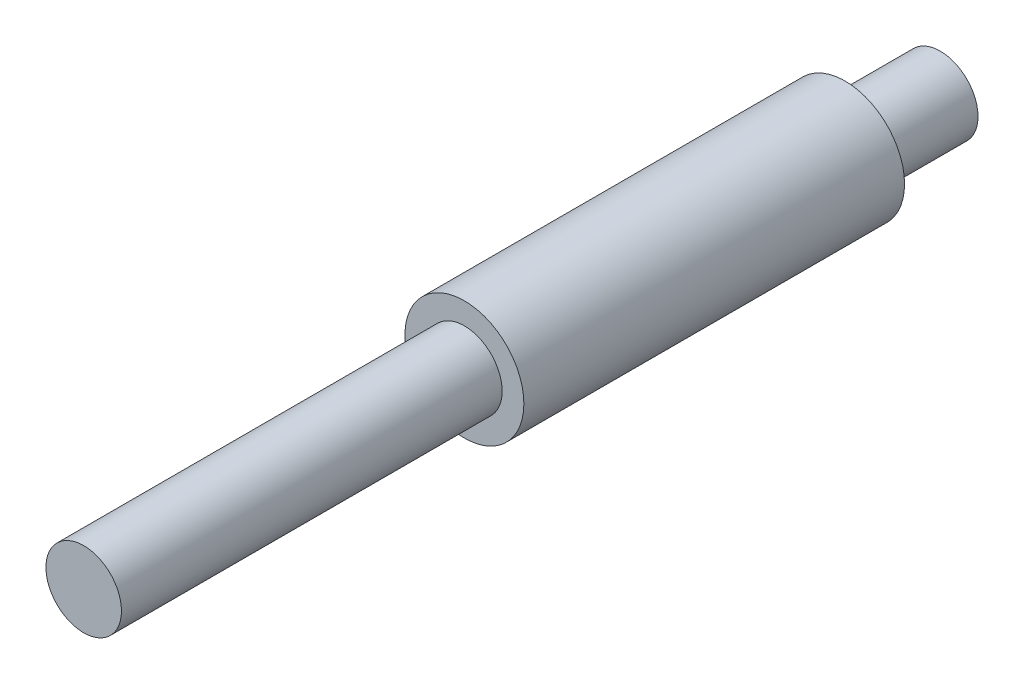
SolidWorks part; units mm, degrees
ref_plane "Plano frontal" through (0, 0, 0) normal (0, 0, 1) x (1, 0, 0)
ref_plane "Plano superior" through (0, 0, 0) normal (0, 1, 0) x (1, 0, 0)
ref_plane "Plano direito" through (0, 0, 0) normal (1, 0, 0) x (0, 0, -1)
sketch "Sketch1" plane through (0, 0, 0) normal (0, 0, 1) x (1, 0, 0)
  circle A0 centre (0, 0) radius 2.5
extrude "Boss-Extrude1" add sketch "Sketch1" along normal blind 16
sketch "Sketch2" plane through (0, 0, 16) normal (0, 0, 1) x (1, 0, 0)
  circle A0 centre (0, 0) radius 1.5875
extrude "Boss-Extrude2" add sketch "Sketch2" along normal blind 16 and the other way blind 20
